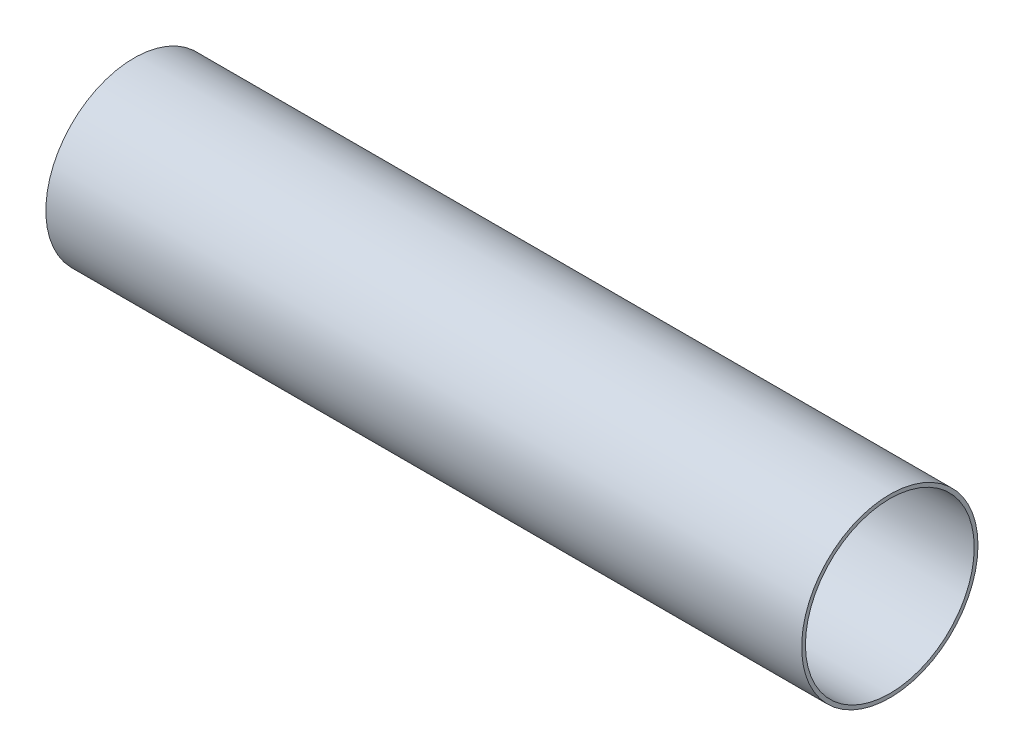
SolidWorks part; units mm, degrees
ref_plane "前视基准面" through (0, 0, 0) normal (0, 0, 1) x (1, 0, 0)
ref_plane "上视基准面" through (0, 0, 0) normal (0, 1, 0) x (1, 0, 0)
ref_plane "右视基准面" through (0, 0, 0) normal (1, 0, 0) x (0, 0, -1)
other "Configuration Table"
sketch "草图1" plane through (0, 0, 0) normal (1, 0, 0) x (0, 0, -1)
  circle A0 centre (0, 0) radius 35
  circle A1 centre (0, 0) radius 33.5
  dimension "D1" = 70
  dimension "D2" = 1.5
extrude "凸台-拉伸1" add sketch "草图1" along normal blind 300
